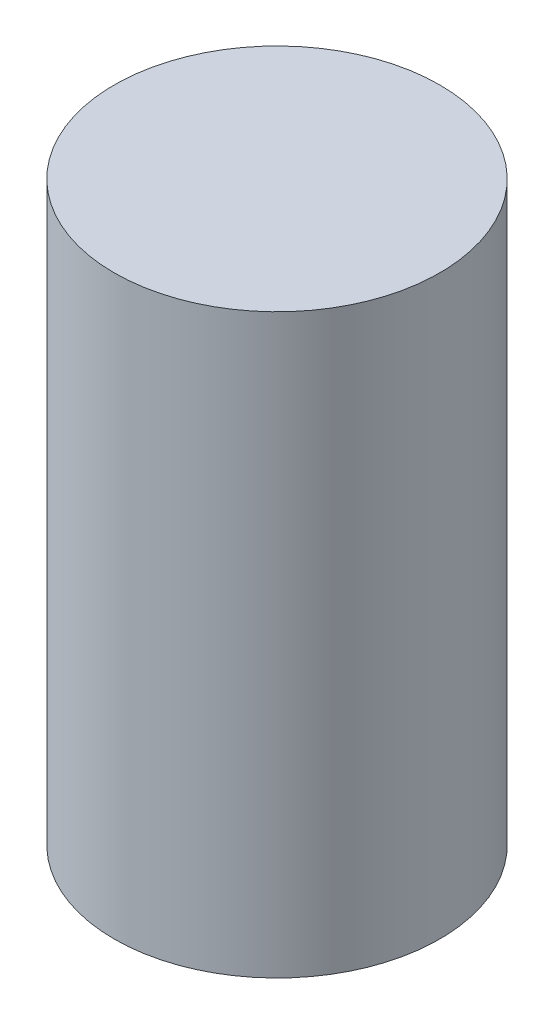
SolidWorks part; units mm, degrees
material "Pure Lead"
ref_plane "Front Plane" through (0, 0, 0) normal (0, 0, 1) x (1, 0, 0)
ref_plane "Top Plane" through (0, 0, 0) normal (0, 1, 0) x (1, 0, 0)
ref_plane "Right Plane" through (0, 0, 0) normal (1, 0, 0) x (0, 0, -1)
sketch "Sketch1" plane through (0, 0, 0) normal (0, 1, 0) x (1, 0, 0)
  circle A0 centre (0, 0) radius 45.72
  dimension "D1" = 91.44
extrude "Extrude1" add sketch "Sketch1" along normal blind 162.052
